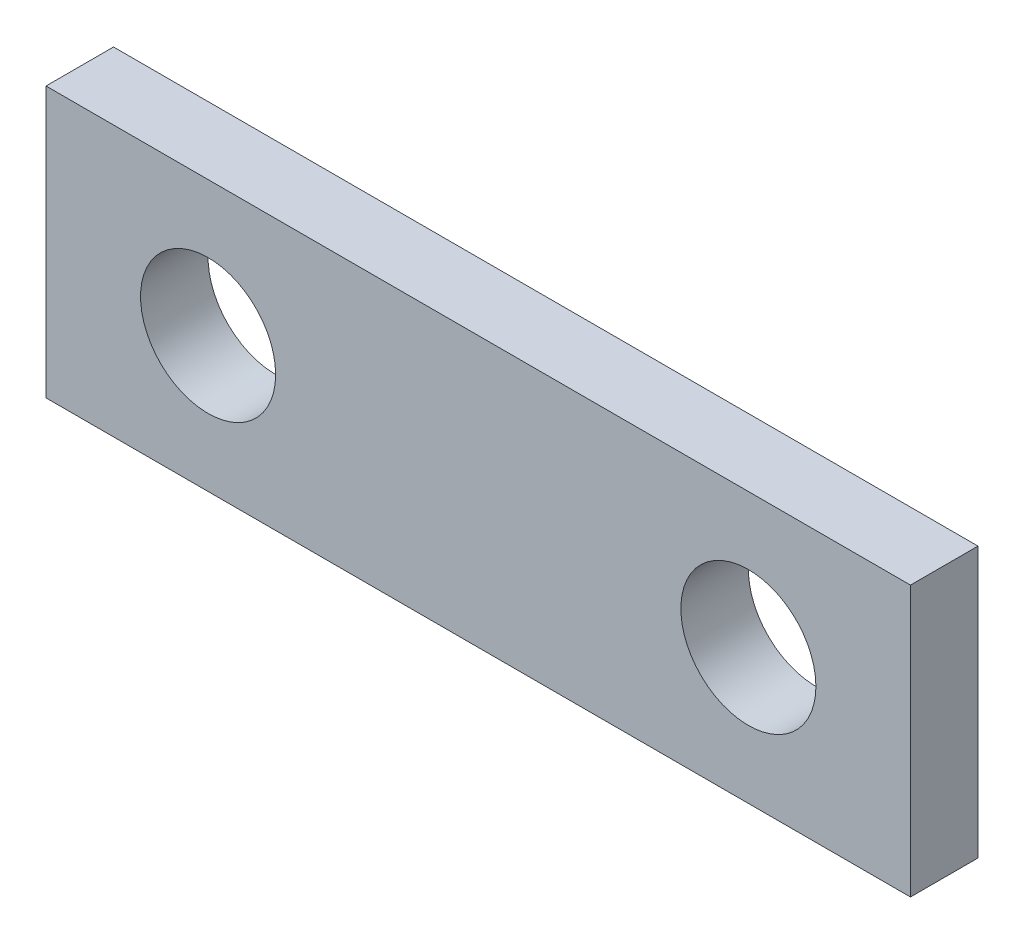
SolidWorks part; units mm, degrees
material "PET"
ref_plane "Front" through (0, 0, 0) normal (0, 0, 1) x (1, 0, 0)
ref_plane "Top" through (0, 0, 0) normal (0, 1, 0) x (1, 0, 0)
ref_plane "Right" through (0, 0, 0) normal (1, 0, 0) x (0, 0, -1)
sketch "Sketch1" plane through (0, 0, 0) normal (0, 0, 1) x (1, 0, 0)
  line L0 (3.81, 3.175) -> (16.51, 3.175) construction
  line L1 (0, 0) -> (20.32, 0)
  line L2 (0, 0) -> (0, 6.35)
  line L3 (0, 6.35) -> (20.32, 6.35)
  line L4 (20.32, 0) -> (20.32, 6.35)
  line L5 (10.16, 3.175) -> (10.16, 0) construction
  line L6 (10.16, 3.175) -> (10.16, 6.35) construction
  circle A0 centre (3.81, 3.175) radius 1.5875
  circle A1 centre (16.51, 3.175) radius 1.5875
  dimension "D4" = 3.175
  dimension "D1" = 20.32
  dimension "D2" = 6.35
  dimension "D3" = 12.7
extrude "Boss-Extrude1" add sketch "Sketch1" along normal blind 1.5875
